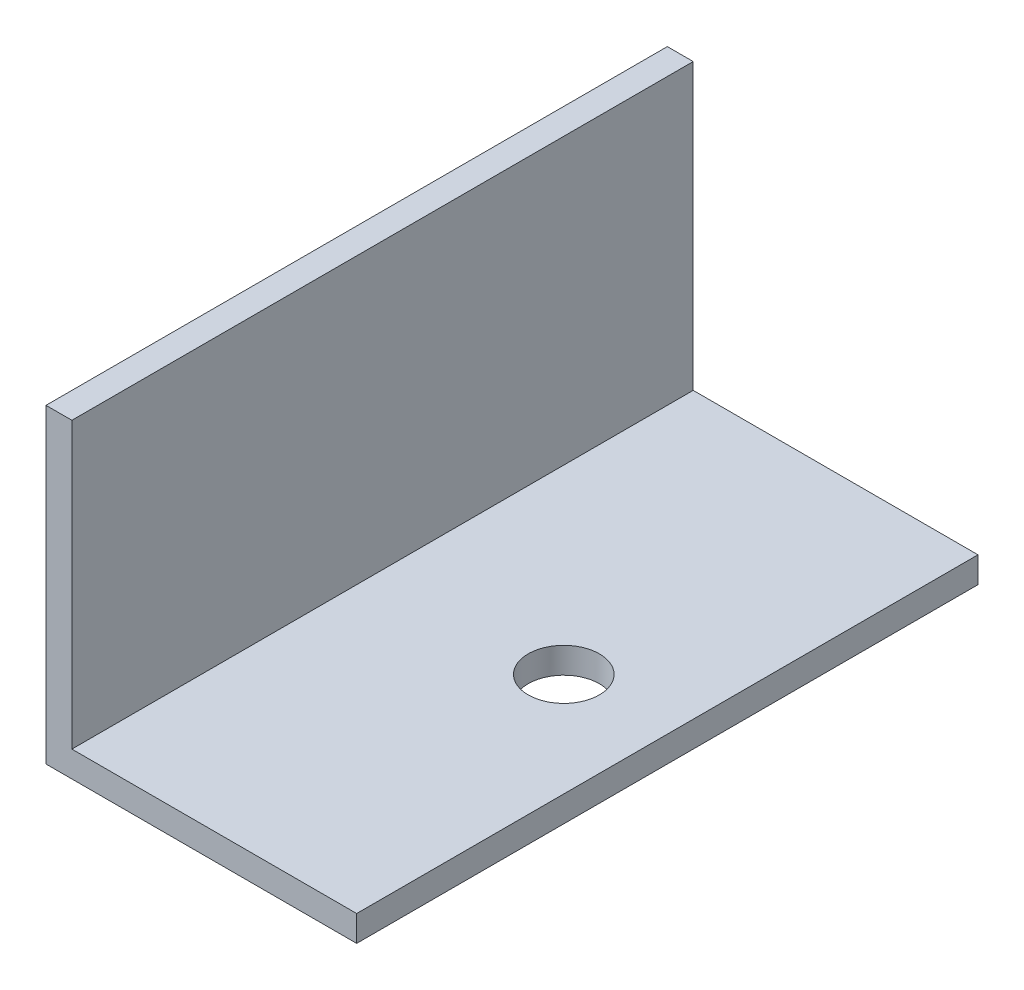
SolidWorks part; units mm, degrees
ref_plane "Front Plane" through (0, 0, 0) normal (0, 0, 1) x (1, 0, 0)
ref_plane "Top Plane" through (0, 0, 0) normal (0, 1, 0) x (1, 0, 0)
ref_plane "Right Plane" through (0, 0, 0) normal (1, 0, 0) x (0, 0, -1)
sketch "Sketch1" plane through (0, 0, 0) normal (0, 0, 1) x (-1, 0, 0)
  line L0 (0, 0) -> (-38.1, 0)
  line L1 (-38.1, 0) -> (-38.1, -3.175)
  line L2 (-38.1, -3.175) -> (-3.175, -3.175)
  line L3 (-3.175, -3.175) -> (-3.175, -38.1)
  line L4 (-3.175, -38.1) -> (0, -38.1)
  line L5 (0, -38.1) -> (0, 0)
  dimension "D1" = 38.1
  dimension "D2" = 38.1
  dimension "D3" = 3.175
extrude "Boss-Extrude1" add sketch "Sketch1" along normal mid plane 76.2
sketch "Sketch2" plane through (0, 0, 0) normal (-1, 0, 0) x (0, 0, 1)
  line L0 (-38.1, 19.05) -> (38.1, 19.05) construction
  line L1 (-38.1, 38.1) -> (-38.1, 0) construction
  line L2 (38.1, 38.1) -> (38.1, 0) construction
  line L3 (0, 38.1) -> (0, 0) construction
  line L4 (38.1, 38.1) -> (-38.1, 38.1) construction
sketch "Sketch3" plane through (0, 3.175, 0) normal (0, 1, 0) x (1, 0, 0)
  line L0 (25.4, 0) -> (0, 0) construction
  line L1 (38.1, -38.1) -> (38.1, 38.1) construction
  circle A0 centre (25.4, 0) radius 4.3656
  dimension "D1" = 8.7312
  dimension "D2" = 12.7
extrude "Cut-Extrude1" cut sketch "Sketch3" against normal up to next
